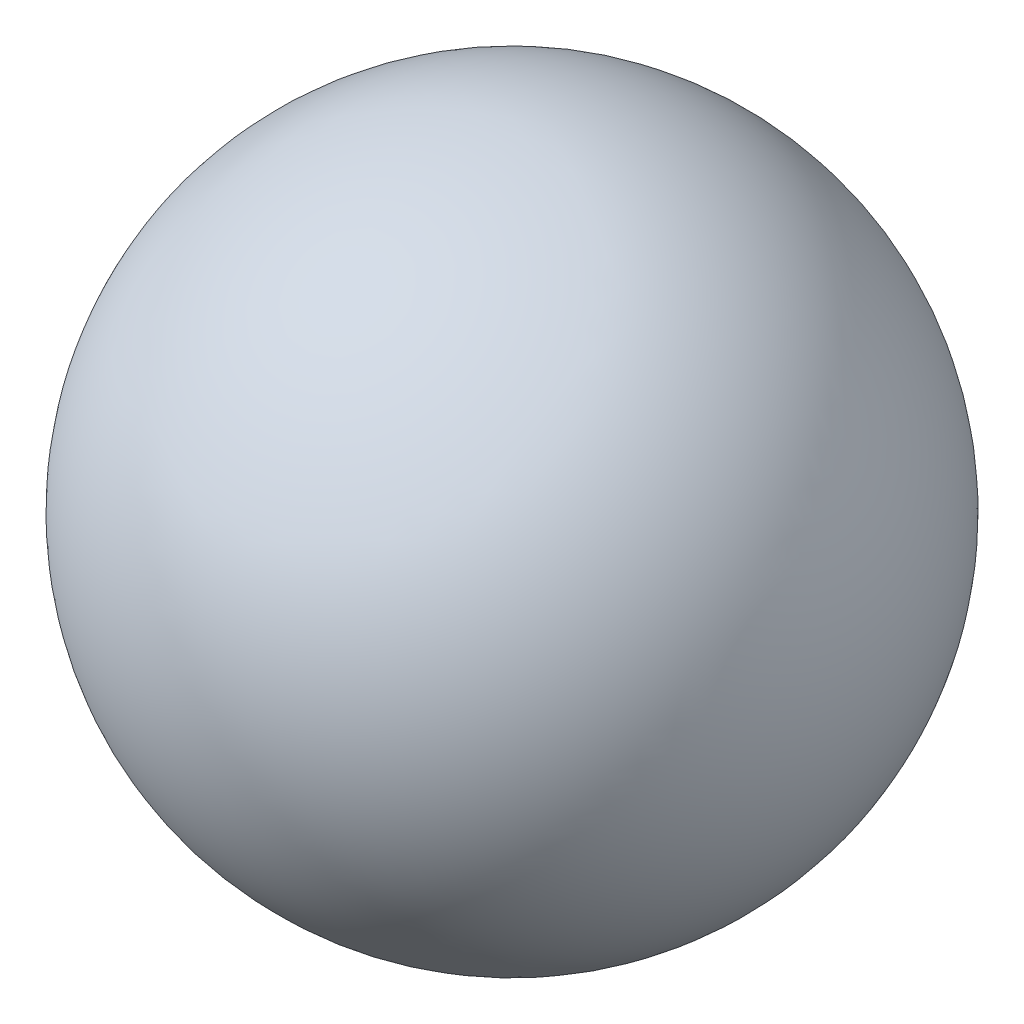
SolidWorks part; units mm, degrees
material "Pure Gold"
ref_plane "Front Plane" through (0, 0, 0) normal (0, 0, 1) x (1, 0, 0)
ref_plane "Top Plane" through (0, 0, 0) normal (0, 1, 0) x (1, 0, 0)
ref_plane "Right Plane" through (0, 0, 0) normal (1, 0, 0) x (0, 0, -1)
sketch "Sketch1" plane through (0, 0, 0) normal (0, 1, 0) x (1, 0, 0)
  line L0 (-50.8, 0) -> (50.8, 0)
  arc A0 (50.8, 0) -> (-50.8, 0) centre (0, 0) cw
  dimension "D1" = 50.8
revolve "Revolve1" add sketch "Sketch1" angle 360 about L0
